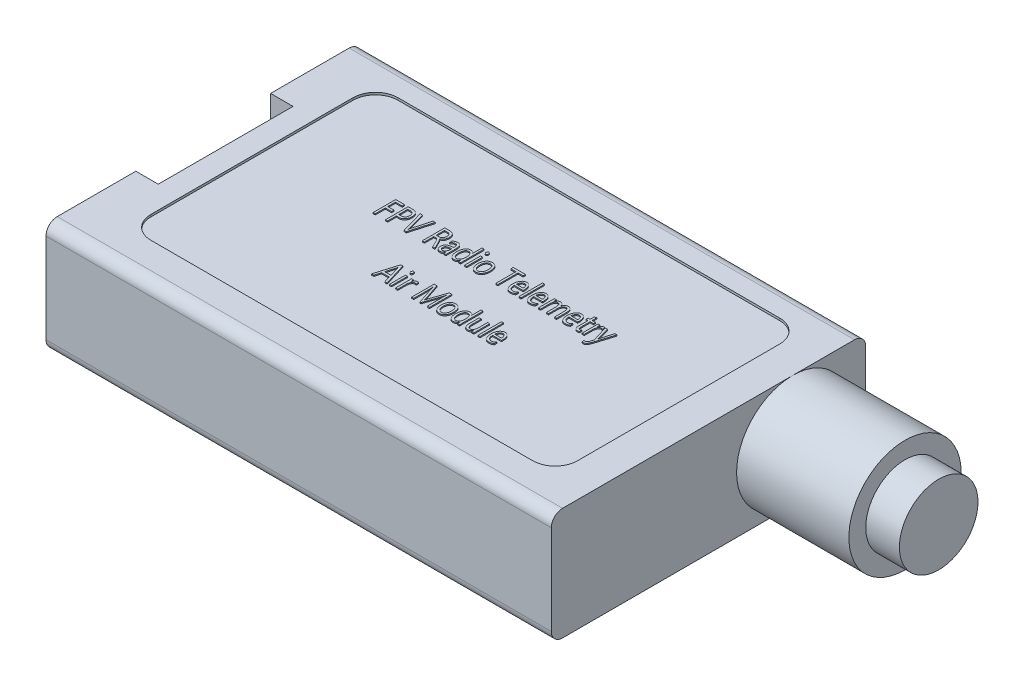
SolidWorks part; units mm, degrees
ref_plane "Front Plane" through (0, 0, 0) normal (0, 0, 1) x (1, 0, 0)
ref_plane "Top Plane" through (0, 0, 0) normal (0, 1, 0) x (1, 0, 0)
ref_plane "Right Plane" through (0, 0, 0) normal (1, 0, 0) x (0, 0, -1)
sketch "Sketch1" plane through (0, 0, 0) normal (0, 1, 0) x (1, 0, 0)
  line L1 (-22.5, -14) -> (22.5, -14)
  line L2 (-22.5, -14) -> (-22.5, 14)
  line L3 (-22.5, 14) -> (22.5, 14)
  line L4 (22.5, -14) -> (22.5, 14)
  line L5 (-22.5, -14) -> (22.5, 14) construction
  line L6 (-22.5, 14) -> (22.5, -14) construction
  point P0 (0, 0)
  dimension "D1" = 45
  dimension "D2" = 28
extrude "Boss-Extrude1" add sketch "Sketch1" along normal blind 10
fillet "Fillet1" radius 1 4 edges at (0, 0, -14) (0, 0, 14) (0, 10, -14) (0, 10, 14)
sketch "Sketch2" plane through (0, 10, 0) normal (0, 1, 0) x (1, 0, 0)
  line L1 (-20.5, -6) -> (-22.5, -6)
  line L2 (-20.5, -6) -> (-20.5, 6)
  line L3 (-20.5, 6) -> (-22.5, 6)
  line L4 (-22.5, -6) -> (-22.5, 6)
  line L5 (-20.5, -6) -> (-22.5, 6) construction
  line L6 (-20.5, 6) -> (-22.5, -6) construction
  point P0 (-21.5, 0)
  dimension "D1" = 12
  dimension "D2" = 2
extrude "Cut-Extrude1" cut sketch "Sketch2" against normal blind 5
sketch "Sketch3" plane through (-20.5, 0, 0) normal (-1, 0, 0) x (0, 0, 1)
  line L0 (6, 5) -> (-6, 5) construction
  line L1 (-4.8892, 8) -> (5.1108, 8)
  line L2 (-4.8892, 8) -> (-4.8892, 5)
  line L3 (-4.8892, 5) -> (5.1108, 5)
  line L4 (5.1108, 8) -> (5.1108, 5)
  line L5 (-4.8892, 8) -> (5.1108, 5) construction
  line L6 (-4.8892, 5) -> (5.1108, 8) construction
  point P0 (0.1108, 6.5)
  dimension "D1" = 10
  dimension "D2" = 3
extrude "Boss-Extrude3" add sketch "Sketch3" along normal blind 1 contours L1 L4 L3 L2
sketch "Sketch4" plane through (-21.5, 0, 0) normal (-1, 0, 0) x (0, 0, 1)
  line L1 (-4.4906, 7.5637) -> (4.6906, 7.5637)
  line L2 (-4.4906, 7.5637) -> (-4.4906, 5.4363)
  line L3 (-4.4906, 5.4363) -> (4.6906, 5.4363)
  line L4 (4.6906, 7.5637) -> (4.6906, 5.4363)
  line L5 (-4.4906, 7.5637) -> (4.6906, 5.4363) construction
  line L6 (-4.4906, 5.4363) -> (4.6906, 7.5637) construction
  point P0 (0.1, 6.5)
extrude "Cut-Extrude2" cut sketch "Sketch4" against normal blind 1
sketch "Sketch7" plane through (-20.5, 0, 0) normal (-1, 0, 0) x (0, 0, 1)
  line L0 (1.75, 6.7) -> (2.25, 6.7)
  line L1 (0.4167, 6.7) -> (0.9167, 6.7)
  line L2 (0.4167, 6.7) -> (0.4167, 5.7)
  line L3 (0.4167, 5.7) -> (0.9167, 5.7)
  line L4 (0.9167, 6.7) -> (0.9167, 5.7)
  line L5 (0.4167, 6.7) -> (0.9167, 5.7) construction
  line L6 (0.4167, 5.7) -> (0.9167, 6.7) construction
  line L7 (1.75, 6.7) -> (1.75, 5.7)
  line L8 (1.75, 5.7) -> (2.25, 5.7)
  line L9 (2.25, 6.7) -> (2.25, 5.7)
  line L10 (1.75, 6.7) -> (2.25, 5.7) construction
  line L11 (1.75, 5.7) -> (2.25, 6.7) construction
  line L12 (-2.25, 6.7) -> (-1.75, 6.7)
  line L13 (-0.9167, 6.7) -> (-0.4167, 6.7)
  line L14 (-0.9167, 6.7) -> (-0.9167, 5.7)
  line L15 (-0.9167, 5.7) -> (-0.4167, 5.7)
  line L16 (-0.4167, 6.7) -> (-0.4167, 5.7)
  line L17 (-0.9167, 6.7) -> (-0.4167, 5.7) construction
  line L18 (-0.9167, 5.7) -> (-0.4167, 6.7) construction
  line L19 (-2.25, 6.7) -> (-2.25, 5.7)
  line L20 (-2.25, 5.7) -> (-1.75, 5.7)
  line L21 (-1.75, 6.7) -> (-1.75, 5.7)
  line L22 (-2.25, 6.7) -> (-1.75, 5.7) construction
  line L23 (-2.25, 5.7) -> (-1.75, 6.7) construction
  point P0 (0.6667, 6.2)
  point P5 (2, 6.2)
  point P10 (-0.6667, 6.2)
  point P15 (-2, 6.2)
  dimension "D1" = 1
  dimension "D2" = 0.5
  dimension "D3" = 1
extrude "Boss-Extrude4" add sketch "Sketch7" along normal blind 2
chamfer "Chamfer1" distance 0.1 angle 70 16 edges at (-22.5, 5.7, -2) (-22.5, 6.2, -2.25) (-22.5, 6.7, -2) (-22.5, 6.2, -1.75) (-22.5, 5.7, 2) (-22.5, 6.2, 1.75) (-22.5, 6.7, 2) (-22.5, 6.2, 2.25) (-22.5, 5.7, 0.6667) (-22.5, 6.2, 0.4167) (-22.5, 6.7, 0.6667) (-22.5, 6.2, 0.9167) (-22.5, 5.7, -0.6667) (-22.5, 6.2, -0.9167) (-22.5, 6.7, -0.6667) (-22.5, 6.2, -0.4167)
sketch "Sketch8" plane through (0, 10, 0) normal (0, 1, 0) x (1, 0, 0)
  line L0 (22.5, -13) -> (22.5, 13) construction
  line L1 (17.5, -10.6566) -> (-16.5, -10.6566)
  line L2 (19.5, -8.6566) -> (19.5, 9.3434)
  line L3 (17.5, 11.3434) -> (-16.5, 11.3434)
  line L4 (-18.5, -8.6566) -> (-18.5, 9.3434)
  arc A0 (19.5, 9.3434) -> (17.5, 11.3434) centre (17.5, 9.3434) ccw
  arc A1 (-16.5, 11.3434) -> (-18.5, 9.3434) centre (-16.5, 9.3434) ccw
  arc A2 (-16.5, -10.6566) -> (-18.5, -8.6566) centre (-16.5, -8.6566) cw
  arc A3 (17.5, -10.6566) -> (19.5, -8.6566) centre (17.5, -8.6566) ccw
  point P8 (19.5, 11.3434)
  point P11 (-18.5, 11.3434)
  point P16 (19.5, -10.6566)
  dimension "D4" = 2
  dimension "D1" = 38
  dimension "D2" = 22
  dimension "D3" = 3
extrude "Cut-Extrude3" cut sketch "Sketch8" against normal blind 0.2
sketch "Sketch9" plane through (0, 9.8, 0) normal (0, 1, 0) x (1, 0, 0)
  text T0 "FPV Radio Telemetry\r\n        Air Module" font "Segoe UI" height 2
  point P1 (0, 0)
sketch "Sketch10" plane through (22.5, 0, 0) normal (1, 0, 0) x (0, 0, -1)
  circle A0 centre (7.5, 5) radius 5
extrude "Boss-Extrude5" add sketch "Sketch10" along normal blind 13
sketch "Sketch11" plane through (35.5, 0, 0) normal (1, 0, 0) x (0, 0, -1)
  circle A0 centre (7.5, 5) radius 3.5
extrude "Cut-Extrude4" cut sketch "Sketch11" against normal blind 3 flip side to cut
extrude "Boss-Extrude6" add sketch "Sketch9" along normal blind 0.1
